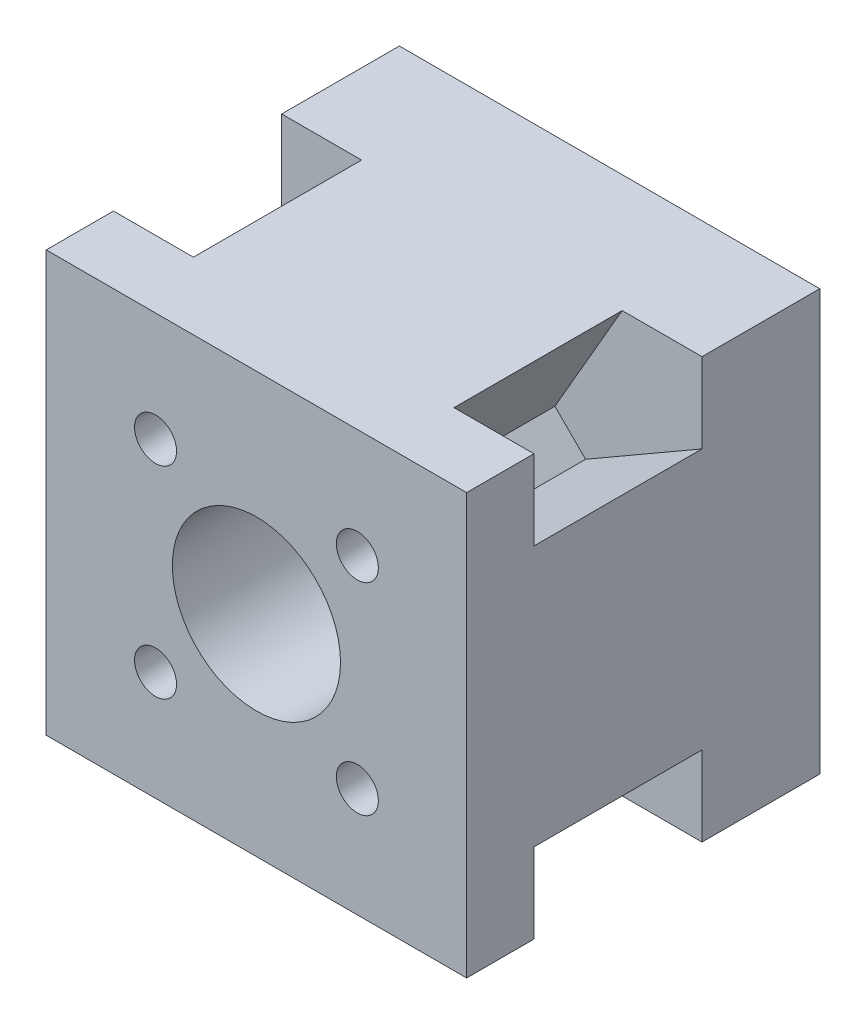
SolidWorks part; units mm, degrees
ref_plane "Front Plane" through (0, 0, 0) normal (0, 0, 1) x (1, 0, 0)
ref_plane "Top Plane" through (0, 0, 0) normal (0, 1, 0) x (1, 0, 0)
ref_plane "Right Plane" through (0, 0, 0) normal (1, 0, 0) x (0, 0, -1)
sketch "Sketch2" plane through (0, 0, 0) normal (0, 0, 1) x (1, 0, 0)
  line L1 (-16.5, -16.5) -> (16.5, -16.5)
  line L2 (-16.5, -16.5) -> (-16.5, 16.5)
  line L3 (-16.5, 16.5) -> (16.5, 16.5)
  line L4 (16.5, -16.5) -> (16.5, 16.5)
  line L5 (-16.5, -16.5) -> (16.5, 16.5) construction
  line L6 (-16.5, 16.5) -> (16.5, -16.5) construction
  line L7 (-25, 25) -> (25, 25)
  line L8 (-25, 25) -> (-25, -25)
  line L9 (-25, -25) -> (25, -25)
  line L10 (25, 25) -> (25, -25)
  line L11 (-25, 25) -> (25, -25) construction
  line L12 (-25, -25) -> (25, 25) construction
  circle A1 centre (-16.5, 16.5) radius 3.5
  circle A2 centre (16.5, 16.5) radius 2.5
  circle A3 centre (-16.5, -16.5) radius 3.5
  circle A4 centre (16.5, -16.5) radius 3.5
  circle A5 centre (0, 0) radius 10
  circle A6 centre (0, 0) radius 10
  point P0 (0, 0)
  dimension "D3" = 20
  dimension "D4" = 7
  dimension "D5" = 7
  dimension "D6" = 7
  dimension "D7" = 5
  dimension "D1" = 33
  dimension "D2" = 33
  dimension "D8" = 50
  dimension "D9" = 50
extrude "Boss-Extrude2" add sketch "Sketch2" along normal blind 14 contours L10 L7 L8 L9 A4 L1 A3 L2 A1 L3 A2 L4 | L3 A1 L2 | L2 A3 L1 | L1 A4 L4 | L4 A2 L3 | L2 A1 L3 | A1 L2 A5 L3 | L1 A3 L2 | A3 L1 A5 L2 | L4 A4 L1 | A4 L4 A5 L1 | L3 A2 L4 | A2 L3 A5 L4 | A5
sketch "Sketch4" plane through (0, 0, 0) normal (0, 0, -1) x (-1, 0, 0)
  circle A0 centre (-16.5, 16.5) radius 2.75
  circle A1 centre (16.5, 16.5) radius 2.75
  circle A2 centre (16.5, -16.5) radius 2.75
  circle A3 centre (-16.5, -16.5) radius 2.75
  dimension "D1" = 5.5
  dimension "D2" = 5.5
  dimension "D3" = 5.5
  dimension "D4" = 5.5
extrude "Cut-Extrude1" cut sketch "Sketch4" against normal blind 12
sketch "Sketch5" plane through (0, 0, 14) normal (0, 0, 1) x (1, 0, 0)
  line L0 (25, 15.5) -> (11.1436, 7.5)
  line L2 (7.5, 11.1436) -> (15.5, 25)
  line L3 (15.5, 25) -> (-15.5, 25)
  line L8 (-15.5, 25) -> (-7.5, 11.1436)
  line L9 (-25, 25) -> (25, 25) construction
  line L11 (-11.1436, 7.5) -> (-25, 15.5)
  line L12 (-25, 25) -> (-25, -25) construction
  line L13 (-25, 15.5) -> (-25, -15.5)
  line L14 (-25, -15.5) -> (-11.1436, -7.5)
  line L17 (-25, -25) -> (25, -25) construction
  line L18 (-15.5, -25) -> (15.5, -25)
  line L21 (11.1436, -7.5) -> (25, -15.5)
  line L22 (25, 25) -> (25, -25) construction
  line L23 (25, -15.5) -> (25, 15.5)
  line L24 (-7.5, 11.1436) -> (-11.1436, 7.5)
  line L25 (7.5, 11.1436) -> (11.1436, 7.5)
  line L26 (-15.5, -25) -> (-7.5, -11.1436)
  line L27 (-11.1436, -7.5) -> (-7.5, -11.1436)
  line L28 (15.5, -25) -> (7.5, -11.1436)
  line L29 (7.5, -11.1436) -> (11.1436, -7.5)
  dimension "D1" = 9.5
  dimension "D2" = 9.5
  dimension "D3" = 120
  dimension "D4" = 120
  dimension "D5" = 16
  dimension "D6" = 16
  dimension "D7" = 9.5
  dimension "D8" = 9.5
  dimension "D9" = 120
  dimension "D10" = 120
  dimension "D11" = 16
  dimension "D12" = 16
  dimension "D13" = 9.5
  dimension "D14" = 9.5
  dimension "D15" = 120
  dimension "D16" = 120
  dimension "D17" = 16
  dimension "D18" = 16
  dimension "D19" = 9.5
  dimension "D20" = 9.5
  dimension "D21" = 120
  dimension "D22" = 120
  dimension "D23" = 16
  dimension "D24" = 16
extrude "Boss-Extrude3" add sketch "Sketch5" along normal blind 20
sketch "Sketch8" plane through (0, 0, 34) normal (0, 0, 1) x (1, 0, 0)
  line L1 (-25, 25) -> (25, 25)
  line L2 (-25, 25) -> (-25, -25)
  line L3 (-25, -25) -> (25, -25)
  line L4 (25, 25) -> (25, -25)
  line L5 (-25, 25) -> (25, -25) construction
  line L6 (-25, -25) -> (25, 25) construction
  point P0 (0, 0)
extrude "Boss-Extrude4" add sketch "Sketch8" along normal blind 8
sketch "Sketch9" plane through (0, 0, 42) normal (0, 0, 1) x (1, 0, 0)
  line L1 (-12, 12) -> (12, 12)
  line L2 (-12, 12) -> (-12, -12)
  line L3 (-12, -12) -> (12, -12)
  line L4 (12, 12) -> (12, -12)
  line L5 (-12, 12) -> (12, -12) construction
  line L6 (-12, -12) -> (12, 12) construction
  circle A0 centre (-12, 12) radius 2.5
  circle A1 centre (-12, -12) radius 2.5
  circle A2 centre (12, -12) radius 2.5
  circle A3 centre (12, 12) radius 2.5
  point P0 (0, 0)
  dimension "D3" = 5
  dimension "D4" = 5
  dimension "D5" = 5
  dimension "D6" = 5
  dimension "D1" = 24
  dimension "D2" = 24
extrude "Cut-Extrude3" cut sketch "Sketch9" against normal up to next contours L4 A3 L1 | L1 A3 L4 | L3 A2 L4 | L4 A2 L3 | L2 A1 L3 | L3 A1 L2 | L1 A0 L2 | L2 A0 L1
sketch "Sketch10" plane through (0, 0, 42) normal (0, 0, 1) x (1, 0, 0)
  circle A0 centre (0, 0) radius 10
extrude "Cut-Extrude4" cut sketch "Sketch10" against normal up to next
